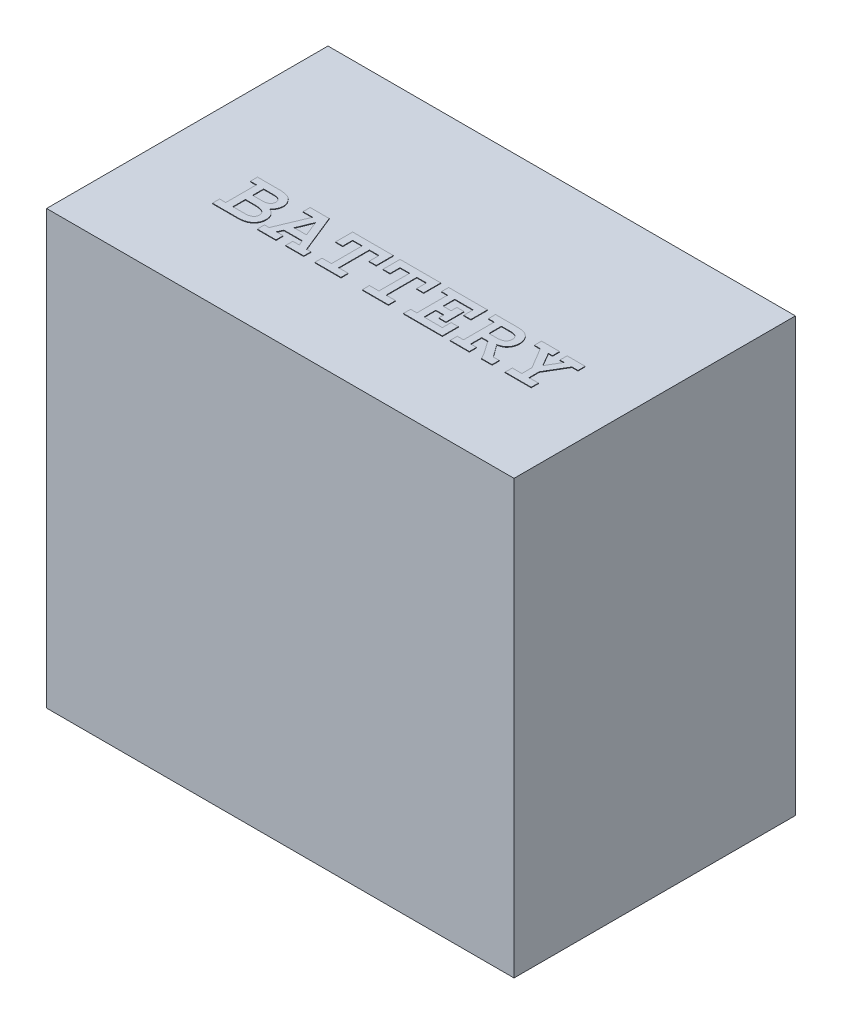
SolidWorks part; units mm, degrees
ref_plane "Front Plane" through (0, 0, 0) normal (0, 0, 1) x (1, 0, 0)
ref_plane "Top Plane" through (0, 0, 0) normal (0, 1, 0) x (1, 0, 0)
ref_plane "Right Plane" through (0, 0, 0) normal (1, 0, 0) x (0, 0, -1)
sketch "Sketch1" plane through (0, 0, 0) normal (0, 0, 1) x (1, 0, 0)
  line L1 (-114.554, -106.045) -> (114.554, -106.045)
  line L2 (-114.554, -106.045) -> (-114.554, 106.045)
  line L3 (-114.554, 106.045) -> (114.554, 106.045)
  line L4 (114.554, -106.045) -> (114.554, 106.045)
  line L5 (-114.554, -106.045) -> (114.554, 106.045) construction
  line L6 (-114.554, 106.045) -> (114.554, -106.045) construction
  point P0 (0, 0)
  dimension "D1" = 212.09
  dimension "D2" = 229.108
extrude "Boss-Extrude1" add sketch "Sketch1" along normal blind 137.922
sketch "Sketch3" plane through (0, 106.045, 0) normal (0, 1, 0) x (1, 0, 0)
  text T0 "<b>BATTERY</b>" font "Courier Std" height in points 100
extrude "Boss-Extrude2" add sketch "Sketch3" along normal blind 0.254
